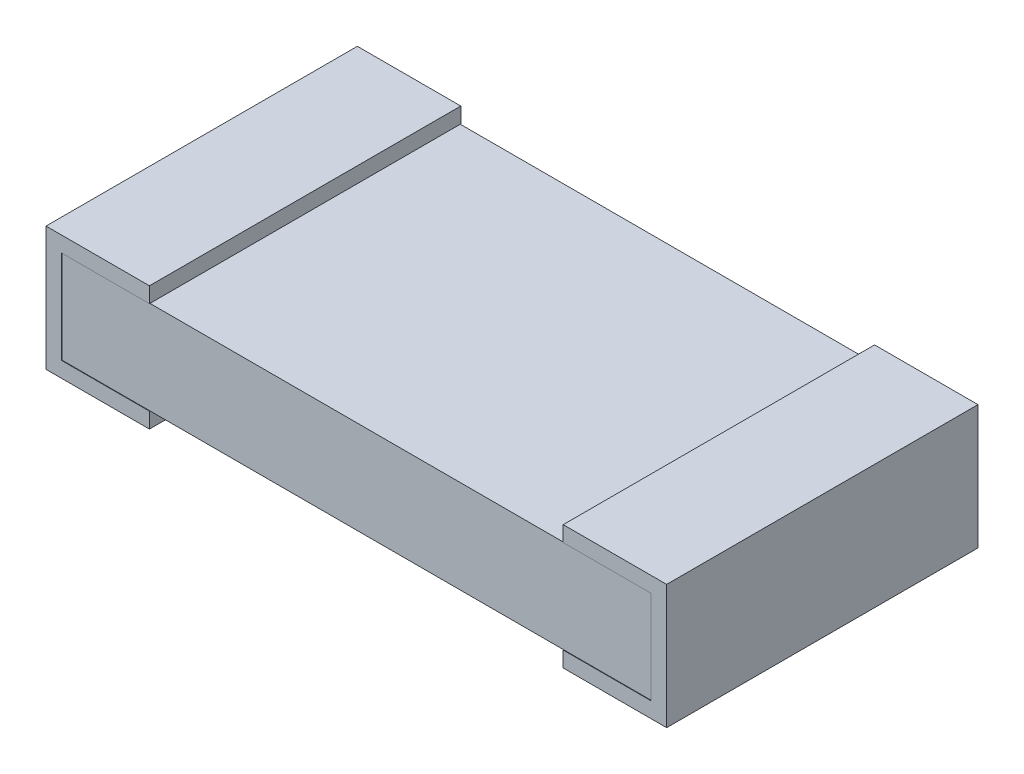
SolidWorks part; units mm, degrees
ref_plane "Front Plane" through (0, 0, 0) normal (0, 0, 1) x (1, 0, 0)
ref_plane "Top Plane" through (0, 0, 0) normal (0, 1, 0) x (1, 0, 0)
ref_plane "Right Plane" through (0, 0, 0) normal (1, 0, 0) x (0, 0, -1)
sketch "Sketch1" plane through (0, 0, 0) normal (0, 0, 1) x (1, 0, 0)
  line L0 (2.9718, 0.0762) -> (0.0762, 0.0762)
  line L1 (2.9718, 0.0762) -> (2.9718, 0.5334)
  line L2 (0.0762, 0.5334) -> (2.9718, 0.5334)
  line L3 (0.0762, 0.5334) -> (0.0762, 0.0762)
  point P4 (1.524, 0.0762)
  dimension "D1" = 2.8956
  dimension "D2" = 0.4572
  dimension "D3" = 0.0762
  dimension "D4" = 0.0762
extrude "Base-Extrude" add sketch "Sketch1" against normal mid plane 1.524
ref_plane "Plane1" through (0, 0, -0.7645) normal (0, 0, -1) x (-1, 0, 0)
sketch "Sketch2" plane through (0, 0, -0.7645) normal (0, 0, -1) x (-1, 0, 0)
  line L0 (0, 0) -> (-0.508, 0)
  line L1 (0, 0) -> (0, 0.6096)
  line L2 (0, 0.6096) -> (-0.508, 0.6096)
  line L3 (-0.508, 0.6096) -> (-0.508, 0.5334)
  line L4 (-2.9718, 0.5334) -> (-0.0762, 0.5334) construction
  line L5 (-0.508, 0) -> (-0.508, 0.0762)
  line L6 (-0.0762, 0.0762) -> (-2.9718, 0.0762) construction
  line L7 (-0.0762, 0.5334) -> (-0.0762, 0.0762) construction
  line L8 (-0.0762, 0.0762) -> (-0.508, 0.0762)
  line L9 (-0.508, 0.5334) -> (-0.0762, 0.5334)
  line L10 (-0.0762, 0.5334) -> (-0.0762, 0.0762)
  dimension "D1" = 0.508
  dimension "D2" = 0.508
  dimension "D3" = 0.0762
extrude "Boss-Extrude1" add sketch "Sketch2" against normal blind 1.5291
ref_plane "Plane2" through (1.524, 0, 0) normal (1, 0, 0) x (0, 0, -1)
mirror "Mirror1" about plane through (1.524, 0, 0) normal (1, 0, 0) of "Boss-Extrude1"
sketch "Component_Outline" plane through (0, 0, 0) normal (0, 1, 0) x (1, 0, 0)
  line L1 (0, -0.7645) -> (3.048, -0.7645)
  line L2 (0, -0.7645) -> (0, 0.7645)
  line L3 (0, 0.7645) -> (3.048, 0.7645)
  line L4 (3.048, -0.7645) -> (3.048, 0.7645)
